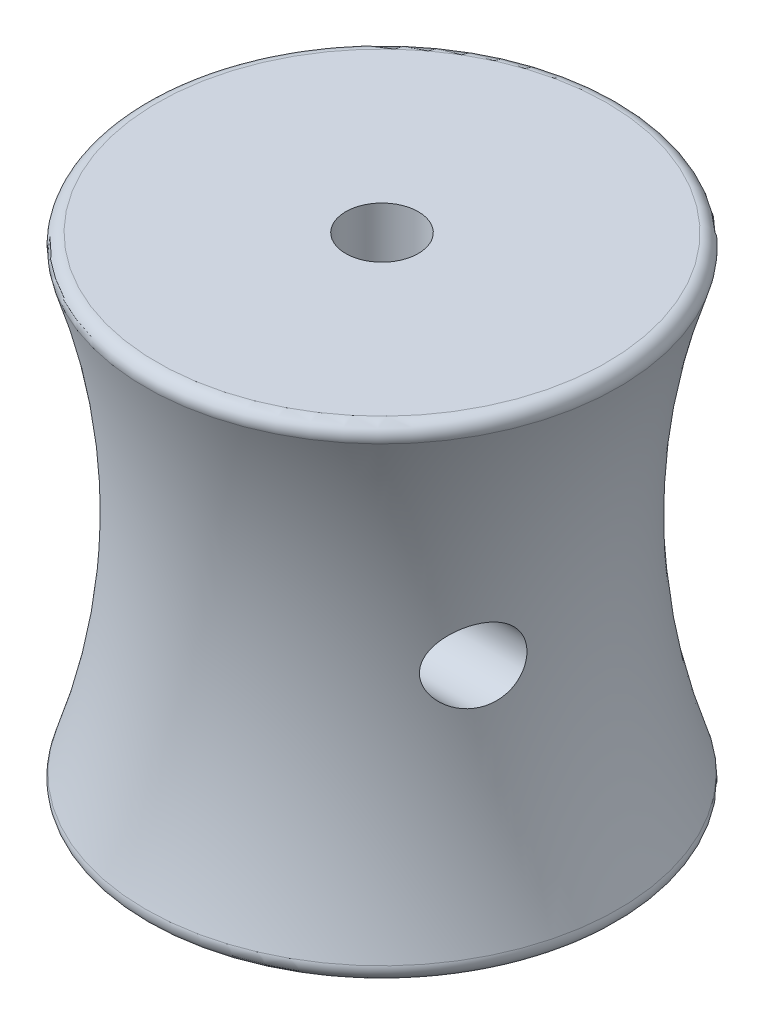
SolidWorks part; units mm, degrees
ref_plane "Plan de face" through (0, 0, 0) normal (0, 0, 1) x (1, 0, 0)
ref_plane "Plan de dessus" through (0, 0, 0) normal (0, 1, 0) x (1, 0, 0)
ref_plane "Plan de droite" through (0, 0, 0) normal (1, 0, 0) x (0, 0, -1)
sketch "Esquisse1" plane through (0, 0, 0) normal (0, 0, 1) x (1, 0, 0)
  line L0 (0, 0) -> (0, 40) construction
  line L2 (-3, 40) -> (-20, 40)
  line L3 (-5, 0) -> (-20, 0)
  line L4 (-5, 0) -> (0, 0) construction
  line L5 (-5, 0) -> (-5, 7)
  line L6 (-5, 7) -> (-3, 7)
  line L7 (-3, 7) -> (-3, 40)
  arc A0 (-20, 40) -> (-20, 0) centre (-75, 20) cw
  point P3 (-45, 19.975)
  point P8 (-1.6892, 39.9218)
  dimension "D1" = 40
  dimension "D2" = 5
  dimension "D3" = 20
  dimension "D4" = 20
  dimension "D5" = 40
  dimension "D6" = 75
  dimension "D7" = 6
  dimension "D8" = 7
revolve "Révolution1" add sketch "Esquisse1" angle 360 about L0
fillet "Congé1" radius 1 2 edges at (0, 0, -20) (0, 40, -20)
sketch "Esquisse2" plane through (0, 0, 0) normal (1, 0, 0) x (0, 0, -1)
  line L0 (-7, 40) -> (-7, 0) construction
  line L2 (18.5904, 40) -> (-18.5904, 40) construction
  line L3 (-18.5904, 0) -> (18.5904, 0) construction
  circle A1 centre (-7, 20) radius 3
  dimension "D1" = 7
  dimension "D2" = 6
extrude "Enlèv. mat.-Extru.1" cut sketch "Esquisse2" against normal through all and the other way through all
